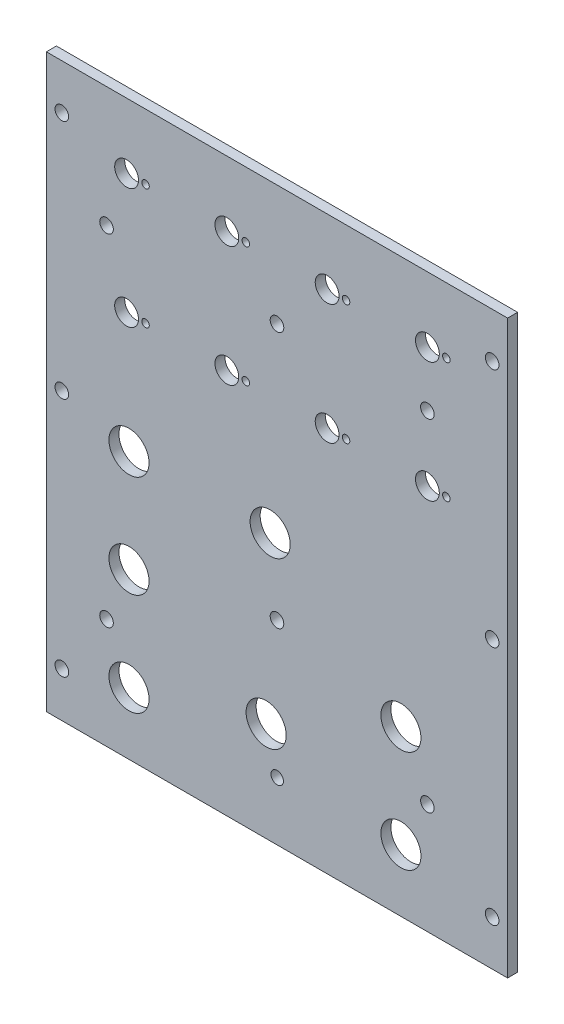
SolidWorks part; units mm, degrees
ref_plane "Front Plane" through (0, 0, 0) normal (0, 0, 1) x (1, 0, 0)
ref_plane "Top Plane" through (0, 0, 0) normal (0, 1, 0) x (1, 0, 0)
ref_plane "Right Plane" through (0, 0, 0) normal (1, 0, 0) x (0, 0, -1)
sketch "Sketch1" plane through (0, 0, 0) normal (0, 0, 1) x (1, 0, 0)
  line L4 (0, 180.975) -> (-146.05, 180.975)
  line L5 (-146.05, 180.975) -> (-146.05, 0)
  line L6 (-146.05, 0) -> (0, 0)
  line L7 (0, 0) -> (0, 180.975)
  line L8 (0, 180.975) -> (-146.05, 180.975)
  line L9 (-146.05, 180.975) -> (-146.05, 0)
  line L10 (-146.05, 0) -> (0, 0)
  line L11 (0, 0) -> (0, 180.975)
  dimension "D1" = 0
extrude "Boss-Extrude1" add sketch "Sketch1" against normal blind 3.175
hole_wizard "#6 Clearance Hole1" positions "Sketch3" profile "Sketch2" hole size "#6" standard "ANSI Inch" end condition through all
sketch "Sketch3" plane through (0, 0, -3.175) normal (0, 0, -1) x (-1, 0, 0)
  point P0 (25.4, 142.875)
  point P7 (73.025, 142.875)
  point P10 (127, 142.875)
  point P13 (25.4, 34.925)
  point P16 (73.025, 61.647)
  point P19 (127, 34.925)
  point P22 (4.8895, 14.2875)
  point P25 (141.1605, 14.2875)
  point P28 (4.8895, 90.4875)
  point P31 (141.1605, 90.4875)
  point P34 (141.1605, 166.6875)
  point P37 (4.8895, 166.6875)
sketch "Sketch2" plane through (-25.4, 142.875, -3.175) normal (1, 0, 0) x (0, 1, 0)
  line L0 (0, 0) -> (0, 3.175)
  line L1 (0, 3.175) -> (2.1526, 3.175)
  line L2 (2.1526, 3.175) -> (2.1526, 0)
  line L5 (2.1526, 0) -> (0, 0)
  line L11 (0, -6.35) -> (0, 107.95) construction
  dimension "Thru Hole Dia." = 4.3053
  dimension "Thru Hole Depth" = 3.175
hole_wizard "19/64 (0.29688) Diameter Hole1" positions "Sketch5" profile "Sketch4" hole size "19/64" standard "ANSI Inch" end condition through all
sketch "Sketch5" plane through (0, 0, -3.175) normal (0, 0, -1) x (-1, 0, 0)
  point P0 (25.4, 160.3248)
  point P3 (57.15, 160.3248)
  point P6 (88.9, 160.3248)
  point P9 (120.65, 160.3248)
  point P12 (25.4, 122.2248)
  point P15 (57.15, 122.2248)
  point P18 (88.9, 122.2248)
  point P21 (120.65, 122.2248)
sketch "Sketch4" plane through (-25.4, 160.3248, -3.175) normal (1, 0, 0) x (0, 1, 0)
  line L0 (0, 0) -> (0, 3.175)
  line L1 (0, 3.175) -> (3.7704, 3.175)
  line L2 (3.7704, 3.175) -> (3.7704, 0)
  line L5 (3.7704, 0) -> (0, 0)
  line L11 (0, -6.35) -> (0, 107.95) construction
  dimension "Thru Hole Dia." = 7.5408
  dimension "Thru Hole Depth" = 3.175
hole_wizard "1/2 (0.5) Diameter Hole1" positions "Sketch7" profile "Sketch6" hole size "1/2" standard "ANSI Inch" end condition through all
sketch "Sketch7" plane through (0, 0, -3.175) normal (0, 0, -1) x (-1, 0, 0)
  point P0 (75.184, 84.455)
  point P3 (119.888, 84.455)
  point P6 (119.888, 52.07)
  point P9 (33.782, 52.07)
  point P12 (33.782, 19.685)
  point P15 (119.888, 19.685)
  point P18 (76.454, 31.496)
sketch "Sketch6" plane through (-75.184, 84.455, -3.175) normal (1, 0, 0) x (0, 1, 0)
  line L0 (0, 0) -> (0, 3.175)
  line L1 (0, 3.175) -> (6.35, 3.175)
  line L2 (6.35, 3.175) -> (6.35, 0)
  line L5 (6.35, 0) -> (0, 0)
  line L11 (0, -6.35) -> (0, 107.95) construction
  dimension "Thru Hole Dia." = 12.7
  dimension "Thru Hole Depth" = 3.175
hole_wizard "5/32 (0.15625) Diameter Hole1" positions "Sketch9" profile "Sketch8" hole size "5/32" standard "ANSI Inch" end condition through all
sketch "Sketch9" plane through (0, 0, -3.175) normal (0, 0, -1) x (-1, 0, 0)
  point P0 (72.9632, 18.4682)
sketch "Sketch8" plane through (-72.9632, 18.4682, -3.175) normal (1, 0, 0) x (0, 1, 0)
  line L0 (0, 0) -> (0, 3.175)
  line L1 (0, 3.175) -> (1.9844, 3.175)
  line L2 (1.9844, 3.175) -> (1.9844, 0)
  line L5 (1.9844, 0) -> (0, 0)
  line L11 (0, -6.35) -> (0, 107.95) construction
  dimension "Thru Hole Dia." = 3.9688
  dimension "Thru Hole Depth" = 3.175
hole_wizard "3/32 (0.09375) Diameter Hole1" positions "Sketch10" profile "Sketch11" hole size "3/32" standard "ANSI Inch" end condition through all
sketch "Sketch10" plane through (0, 0, -3.175) normal (0, 0, -1) x (-1, 0, 0)
  point P0 (19.4, 160.3248)
  point P2 (51.15, 160.3248)
  point P4 (82.9, 160.3248)
  point P6 (114.65, 160.3248)
  point P8 (114.65, 122.2248)
  point P10 (82.9, 122.2248)
  point P12 (51.15, 122.2248)
  point P14 (19.4, 122.2248)
sketch "Sketch11" plane through (-19.4, 160.3248, -3.175) normal (1, 0, 0) x (0, 1, 0)
  line L0 (0, 0) -> (0, 3.175)
  line L1 (0, 3.175) -> (1.1906, 3.175)
  line L2 (1.1906, 3.175) -> (1.1906, 0)
  line L5 (1.1906, 0) -> (0, 0)
  line L11 (0, -6.35) -> (0, 107.95) construction
  dimension "Thru Hole Dia." = 2.3812
  dimension "Thru Hole Depth" = 3.175
